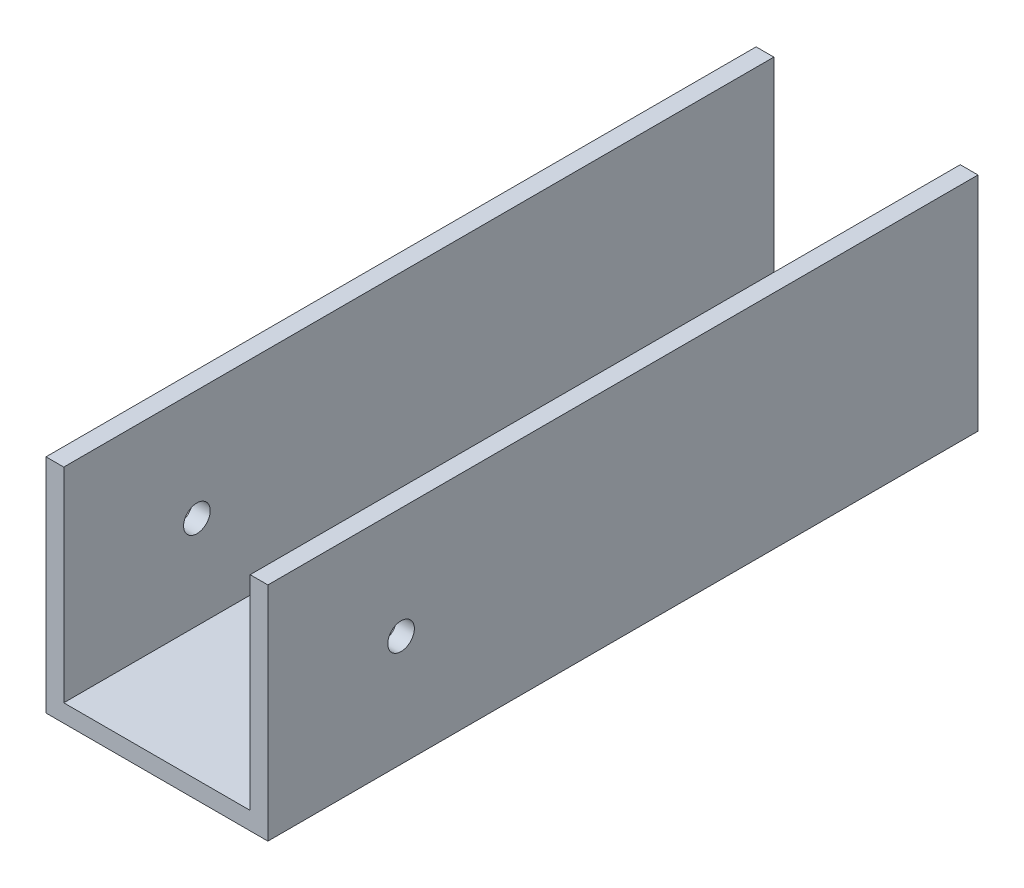
SolidWorks part; units mm, degrees
material "1060 Alloy"
ref_plane "Front" through (0, 0, 0) normal (0, 0, 1) x (1, 0, 0)
ref_plane "Top" through (0, 0, 0) normal (0, 1, 0) x (1, 0, 0)
ref_plane "Right" through (0, 0, 0) normal (1, 0, 0) x (0, 0, -1)
sketch "Sketch2" plane through (0, 0, 0) normal (0, 0, 1) x (1, 0, 0)
  line L0 (23, 25) -> (25, 25)
  line L1 (0, 0) -> (25, 0)
  line L2 (0, 0) -> (0, 25)
  line L3 (0, 25) -> (2, 25)
  line L4 (25, 0) -> (25, 25)
  line L6 (2, 25) -> (2, 2)
  line L7 (2, 2) -> (23, 2)
  line L8 (23, 25) -> (23, 2)
  dimension "D1" = 25
  dimension "D2" = 25
  dimension "D3" = 2
  dimension "D4" = 2
  dimension "D5" = 2
extrude "Boss-Extrude1" add sketch "Sketch2" along normal blind 80
sketch "Sketch3" plane through (25, 0, 0) normal (1, 0, 0) x (0, 0, -1)
  line L0 (-80, 0) -> (-80, 25) construction
  line L1 (-80, 25) -> (0, 25) construction
  circle A0 centre (-65, 12.5) radius 1.5
  dimension "D3" = 3
  dimension "D1" = 15
  dimension "D2" = 12.5
extrude "Cut-Extrude1" cut sketch "Sketch3" against normal up to surface (25 mm away) up to face at (0, 12.5, 40)
sketch "Sketch4" plane through (0, 0, 0) normal (0, -1, 0) x (1, 0, 0)
  line L0 (25, 40) -> (-49975, 40) construction
  line L1 (25, 80) -> (25, 0) construction
  line L2 (0, 80) -> (0, 0) construction
  line L3 (0, 80) -> (25, 80) construction
  circle A0 centre (12.5, 60) radius 3
  circle A1 centre (12.5, 20) radius 3
  point P6 (25, 40)
  point P9 (0, 40)
  dimension "D1" = 6
  dimension "D2" = 12.5
  dimension "D3" = 20
extrude "Cut-Extrude2" cut sketch "Sketch4" against normal up to next
